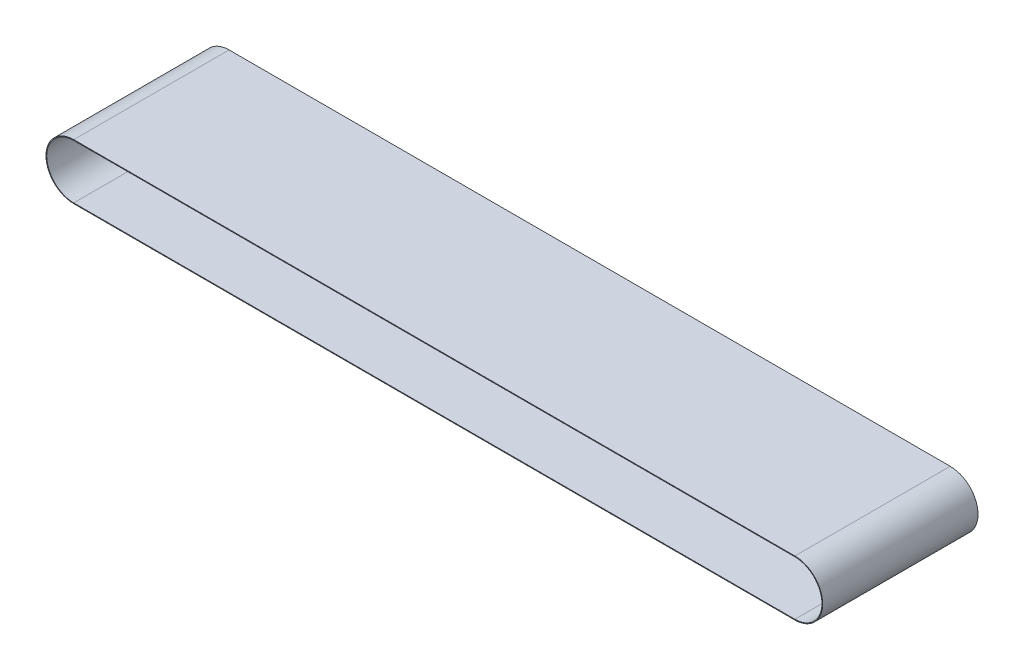
SolidWorks part; units mm, degrees
ref_plane "Front Plane" through (0, 0, 0) normal (0, 0, 1) x (1, 0, 0)
ref_plane "Top Plane" through (0, 0, 0) normal (0, 1, 0) x (1, 0, 0)
ref_plane "Right Plane" through (0, 0, 0) normal (1, 0, 0) x (0, 0, -1)
sketch "Sketch1" plane through (0, 0, 0) normal (0, 0, 1) x (1, 0, 0)
  line L0 (-255.3, 19.65) -> (255.3, 19.65)
  line L1 (-255.3, 0) -> (255.3, 0) construction
  line L2 (-255.3, 19.15) -> (255.3, 19.15)
  line L3 (-255.3, -19.15) -> (255.3, -19.15)
  line L4 (-255.3, -19.65) -> (255.3, -19.65)
  arc A0 (-255.3, 19.15) -> (-255.3, -19.15) centre (-255.3, 0) ccw
  arc A1 (255.3, -19.15) -> (255.3, 19.15) centre (255.3, 0) ccw
  arc A2 (255.3, -19.65) -> (255.3, 19.65) centre (255.3, 0) ccw
  arc A3 (-255.3, 19.65) -> (-255.3, -19.65) centre (-255.3, 0) ccw
  point P5 (0, 0)
  dimension "D2" = 19.15
  dimension "D1" = 510.6
  dimension "D3" = 0.5
extrude "Boss-Extrude1" add sketch "Sketch1" along normal blind 110
